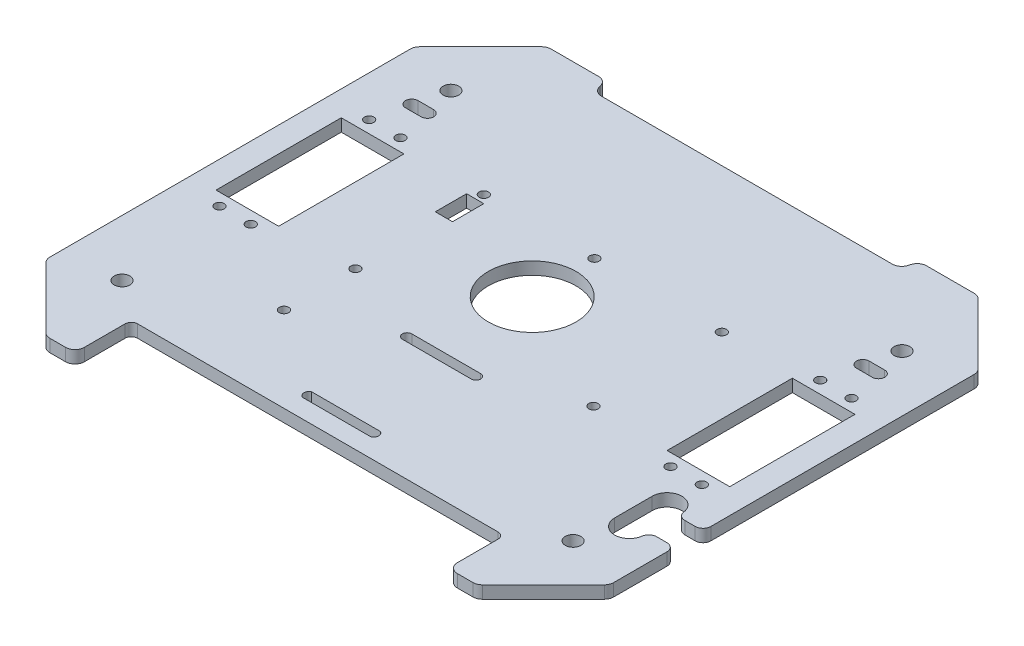
SolidWorks part; units mm, degrees
material "Acrylic (Medium-high impact)"
ref_plane "Front Plane" through (0, 0, 0) normal (0, 0, 1) x (1, 0, 0)
ref_plane "Top Plane" through (0, 0, 0) normal (0, 1, 0) x (1, 0, 0)
ref_plane "Right Plane" through (0, 0, 0) normal (1, 0, 0) x (0, 0, -1)
sketch "Sketch1" plane through (0, 0, 0) normal (0, 1, 0) x (1, 0, 0)
  line L0 (0, -78.7726) -> (0, 81.2274)
  line L1 (67.5442, -78.7726) -> (0, -78.7726)
  line L2 (90, -56.3167) -> (90, 58.7716)
  line L3 (67.5442, 81.2274) -> (0, 81.2274)
  line L4 (-22, 1.2274) -> (22, 1.2274) construction
  line L7 (89.1213, 60.8929) -> (69.6655, 80.3487)
  line L8 (89.1213, -58.4381) -> (69.6655, -77.8939)
  arc A0 (69.6655, 80.3487) -> (67.5442, 81.2274) centre (67.5442, 78.2274) ccw
  arc A1 (89.1213, 60.8929) -> (90, 58.7716) centre (87, 58.7716) cw
  arc A2 (89.1213, -58.4381) -> (90, -56.3167) centre (87, -56.3167) ccw
  arc A3 (69.6655, -77.8939) -> (67.5442, -78.7726) centre (67.5442, -75.7726) cw
  point P7 (68.7868, 81.2274)
  point P15 (90, 60.0142)
  point P18 (90, -57.5594)
  point P21 (68.7868, -78.7726)
  dimension "D8" = 3
  dimension "D1" = 135
  dimension "D2" = 135
  dimension "D3" = 160
  dimension "D4" = 30
  dimension "D5" = 30
  dimension "D6" = 90
  dimension "D7" = 80
extrude "Boss-Extrude1" add sketch "Sketch1" along normal blind 4
sketch "Sketch6" plane through (0, 4, 0) normal (0, 1, 0) x (1, 0, 0)
  line L1 (62.0096, -11.2726) -> (62.0096, 28.7274) construction
  line L2 (82.0096, -11.2726) -> (62.0096, -11.2726) construction
  line L3 (62.0096, 28.7274) -> (82.0096, 28.7274) construction
  line L4 (82.0096, 28.7274) -> (82.0096, -11.2726) construction
  line L9 (62.0096, -11.2726) -> (62.0096, 28.7274)
  line L11 (82.0096, -11.2726) -> (62.0096, -11.2726)
  line L16 (62.0096, 28.7274) -> (82.0096, 28.7274)
  line L17 (82.0096, 28.7274) -> (82.0096, -11.2726)
  circle A1 centre (67.0096, 32.6274) radius 1.5
  circle A2 centre (77.0096, 32.6274) radius 1.5
  circle A3 centre (77.0096, -15.1726) radius 1.5
  circle A4 centre (67.0096, -15.1726) radius 1.5
  circle A6 centre (72.0096, 53.7274) radius 2.5
  circle A11 centre (72.0096, -51.2726) radius 2.5
  dimension "D1" = 40
  dimension "D5" = 3
  dimension "D3" = 5
  dimension "D2" = 20
extrude "Cut-Extrude1" cut sketch "Sketch6" against normal up to next
sketch "Sketch7" plane through (0, 4, 0) normal (0, 1, 0) x (1, 0, 0)
  line L0 (-0.753, -53.2726) -> (10.247, -53.2726) construction
  line L1 (-0.753, -51.7726) -> (11, -51.7726)
  line L2 (-0.753, -54.7726) -> (11, -54.7726)
  line L3 (-0.753, -51.7726) -> (-0.753, -54.7726)
  line L4 (0, -21.2726) -> (11, -21.2726) construction
  line L5 (0, -19.7726) -> (11, -19.7726)
  line L6 (0, -22.7726) -> (11, -22.7726)
  line L7 (0, -19.7726) -> (0, -22.7726)
  line L12 (0, 81.2274) -> (0, -78.7726) construction
  line L13 (69.5096, 43.7274) -> (74.5096, 43.7274) construction
  line L14 (69.5096, 45.7274) -> (74.5096, 45.7274)
  line L15 (69.5096, 41.7274) -> (74.5096, 41.7274)
  line L16 (82.0096, -11.2726) -> (82.0096, 28.7274) construction
  line L18 (0, -78.7726) -> (67.5442, -78.7726) construction
  line L23 (0, -78.7726) -> (67.5442, -78.7726) construction
  line L28 (62.5442, -78.7726) -> (67.5442, -78.7726)
  line L29 (82.0096, 28.7274) -> (62.0096, 28.7274) construction
  line L34 (0, 76.2274) -> (46.4319, 76.2274)
  line L35 (67.5442, 81.2274) -> (0, 81.2274) construction
  line L38 (0, 76.2274) -> (0, 87.2274)
  line L39 (0, 87.2274) -> (56.0737, 87.2274)
  line L40 (56.0737, 87.2274) -> (56.0737, 81.2274)
  line L41 (49.3297, 78.451) -> (49.4779, 79.0039)
  line L42 (52.3756, 81.2274) -> (56.0737, 81.2274)
  line L84 (59.5442, -75.7726) -> (59.5442, -62.7726)
  line L85 (57.5442, -60.7726) -> (0, -60.7726)
  arc A0 (11, -22.7726) -> (11, -19.7726) centre (11, -21.2726) ccw
  arc A1 (11, -54.7726) -> (11, -51.7726) centre (10.247, -53.2726) ccw
  arc A8 (46.4319, 76.2274) -> (49.3297, 78.451) centre (46.4319, 79.2274) ccw
  arc A9 (69.5096, 45.7274) -> (69.5096, 41.7274) centre (69.5096, 43.7274) ccw
  arc A10 (74.5096, 41.7274) -> (74.5096, 45.7274) centre (74.5096, 43.7274) ccw
  circle A12 centre (38, 30.2274) radius 1.5
  circle A14 centre (38, -10.7726) radius 1.5
  arc A21 (59.5442, -75.7726) -> (62.5442, -78.7726) centre (62.5442, -75.7726) ccw
  arc A22 (49.4779, 79.0039) -> (52.3756, 81.2274) centre (52.3756, 78.2274) cw
  arc A55 (57.5442, -60.7726) -> (59.5442, -62.7726) centre (57.5442, -62.7726) cw
  point P19 (54.5434, -27.7726)
  point P38 (72.0096, 43.7274)
  point P40 (54.5434, -57.7726)
  point P49 (72.0096, 28.7274)
  point P58 (54.5434, -37.7726)
  point P80 (59.5442, -78.7726)
  point P81 (23.4762, -78.7726)
  point P89 (35, -78.7726)
  point P101 (50.0737, 81.2274)
  point P217 (59.5442, -60.7726)
  point P218 (50.5, -66.7726)
  point P225 (50.5, -66.7726)
  point P232 (50.5, -66.7726)
  point P239 (50.5, -66.7726)
  point P246 (50.5, -66.7726)
  point P253 (50.5, -66.7726)
  point P260 (50.5, -66.7726)
  point P267 (50.5, -66.7726)
  point P274 (50.5, -66.7726)
  point P281 (50.5, -66.7726)
  point P288 (50.5, -66.7726)
  point P295 (50.5, -66.7726)
  point P309 (54.5434, -57.7726)
  point P316 (54.5434, -57.7726)
  point P323 (54.5434, -57.7726)
  point P330 (54.5434, -57.7726)
  point P337 (54.5434, -57.7726)
  point P344 (54.5434, -57.7726)
  point P351 (54.5434, -57.7726)
  point P358 (54.5434, -57.7726)
  point P365 (54.5434, -57.7726)
  point P372 (54.5434, -57.7726)
  point P379 (54.5434, -57.7726)
  point P386 (54.5434, -57.7726)
  point P393 (54.5434, -57.7726)
  point P400 (54.5434, -57.7726)
  point P407 (54.5434, -57.7726)
  point P414 (54.5434, -57.7726)
  point P421 (54.5434, -57.7726)
  point P428 (54.5434, -57.7726)
  point P435 (54.5434, -57.7726)
  point P442 (54.5434, -57.7726)
  point P449 (54.5434, -57.7726)
  point P456 (54.5434, -57.7726)
  point P463 (54.5434, -57.7726)
  point P470 (54.5434, -57.7726)
  point P477 (54.5434, -57.7726)
  point P484 (54.5434, -57.7726)
  point P491 (54.5434, -27.7726)
  point P498 (54.5434, -37.7726)
  point P505 (54.5434, -57.7726)
  point P512 (53.6101, -31.1059)
  point P519 (53.6101, -44.4392)
  point P526 (53.6101, -71.1059)
  point P533 (53.6101, -31.1059)
  point P540 (53.6101, -44.4392)
  point P547 (53.6101, -71.1059)
  point P554 (53.8601, -29.4392)
  point P561 (53.8601, -41.1059)
  point P568 (53.8601, -64.4392)
  point P575 (53.8601, -29.4392)
  point P582 (53.8601, -41.1059)
  point P589 (53.8601, -64.4392)
  point P596 (53.8601, -29.4392)
  point P603 (53.8601, -41.1059)
  point P610 (53.8601, -64.4392)
  point P617 (53.8601, -29.4392)
  point P624 (53.8601, -41.1059)
  point P631 (53.8601, -64.4392)
  point P638 (53.8601, -29.4392)
  point P645 (53.8601, -41.1059)
  point P652 (53.8601, -64.4392)
  point P659 (53.8601, -29.4392)
  point P666 (53.8601, -41.1059)
  point P673 (53.8601, -64.4392)
  point P680 (53.8601, -29.4392)
  point P687 (53.8601, -41.1059)
  point P694 (53.8601, -64.4392)
  point P701 (53.8601, -29.4392)
  point P708 (53.8601, -41.1059)
  point P715 (53.8601, -64.4392)
  point P722 (53.8601, -29.4392)
  point P729 (53.8601, -41.1059)
  point P736 (53.8601, -64.4392)
  point P743 (53.8601, -29.4392)
  point P750 (53.8601, -41.1059)
  point P757 (53.8601, -64.4392)
  point P764 (53.8601, -29.4392)
  point P771 (53.8601, -41.1059)
  point P778 (53.8601, -64.4392)
  point P785 (53.8601, -29.4392)
  point P792 (53.8601, -41.1059)
  point P799 (53.8601, -64.4392)
  point P806 (53.8601, -29.4392)
  point P813 (53.8601, -41.1059)
  point P820 (53.8601, -64.4392)
  point P827 (53.8601, -29.4392)
  point P834 (53.8601, -41.1059)
  point P841 (53.8601, -64.4392)
  point P848 (53.8601, -29.4392)
  point P855 (53.8601, -41.1059)
  point P862 (53.8601, -64.4392)
  dimension "D18" = 3
  dimension "D7" = 3
  dimension "D16" = 6
  dimension "D5" = 5
  dimension "D25" = 6
  dimension "D28" = 255
  dimension "D39" = 8
  dimension "D40" = 18
  dimension "D9" = 38
  dimension "D6" = 41
  dimension "D8" = 51
  dimension "D10" = 4
  dimension "D11" = 5
  dimension "D17" = 10
  dimension "D19" = 15
  dimension "D13" = 3
  dimension "D15" = 6
  dimension "D20" = 3
  dimension "D21" = 0
  dimension "D22" = 11
  dimension "D23" = 32
  dimension "D12" = 11
extrude "Cut-Extrude2" cut sketch "Sketch7" against normal through all
mirror "Mirror1" about plane through (0, 4, 78.7726) normal (1, 0, 0) of "Cut-Extrude2", "Cut-Extrude1", "Boss-Extrude1"
sketch "Sketch8" plane through (0, 4, 0) normal (0, 1, 0) x (1, 0, 0)
  line L1 (-41, 27.7274) -> (-35.5, 27.7274)
  line L2 (-41, 27.7274) -> (-41, 17.7274)
  line L3 (-41, 17.7274) -> (-35.5, 17.7274)
  line L4 (-35.5, 27.7274) -> (-35.5, 17.7274)
  line L14 (62.0096, 28.7274) -> (62.0096, -11.2726) construction
  line L18 (77.0096, -26.2726) -> (77.0096, -38.2726) construction
  line L19 (90, -25.2726) -> (90, -39.2726)
  line L20 (72.2756, -26.2726) -> (72.2756, -38.2726)
  line L21 (62.0096, -11.2726) -> (82.0096, -11.2726) construction
  line L22 (84.1742, -27.7726) -> (87.5, -27.7726)
  line L26 (90, -56.3167) -> (90, 58.7716) construction
  line L29 (87.5, -36.7726) -> (84.1742, -36.7726)
  circle A0 centre (-38, 30.2274) radius 1.5 construction
  arc A11 (81.6982, -25.6182) -> (72.2756, -26.2726) centre (77.0096, -26.2726) ccw
  arc A12 (72.2756, -38.2726) -> (81.6982, -38.927) centre (77.0096, -38.2726) ccw
  arc A13 (81.6982, -38.927) -> (84.1742, -36.7726) centre (84.1742, -39.2726) cw
  arc A14 (81.6982, -25.6182) -> (84.1742, -27.7726) centre (84.1742, -25.2726) ccw
  arc A18 (87.5, -36.7726) -> (90, -39.2726) centre (87.5, -39.2726) cw
  arc A19 (87.5, -27.7726) -> (90, -25.2726) centre (87.5, -25.2726) ccw
  point P40 (77.0096, -32.2726)
  point P67 (90, -27.7726)
  dimension "D4" = 12.5
  dimension "D15" = 9
  dimension "D16" = 2.5
  dimension "D18" = 2.5
  dimension "D19" = 2.5
  dimension "D1" = 5.5
  dimension "D2" = 10
  dimension "D3" = 2.5
  dimension "D12" = 15
  dimension "D13" = 15
  dimension "D14" = 12
  dimension "D17" = 4.5
  dimension "D20" = 0
extrude "Cut-Extrude3" cut sketch "Sketch8" against normal through all
sketch "Sketch9" plane through (0, 4, 0) normal (0, 1, 0) x (1, 0, 0)
  line L0 (-38, 30.2274) -> (-2.69, 30.2274) construction
  circle A0 centre (-2.69, 30.2274) radius 1.5
  circle A1 centre (-38, 30.2274) radius 1.5 construction
  circle A2 centre (-38, -33.5726) radius 1.5
  circle A3 centre (-38, -10.7726) radius 1.5 construction
  circle A4 centre (-2.06, 9.7274) radius 14
  dimension "D1" = 35.31
  dimension "D2" = 22.8
  dimension "D5" = 28
  dimension "D3" = 20.5
  dimension "D4" = 35.94
extrude "Cut-Extrude4" cut sketch "Sketch9" against normal through all
equation "\"D9@Sketch7\"=76/2"
